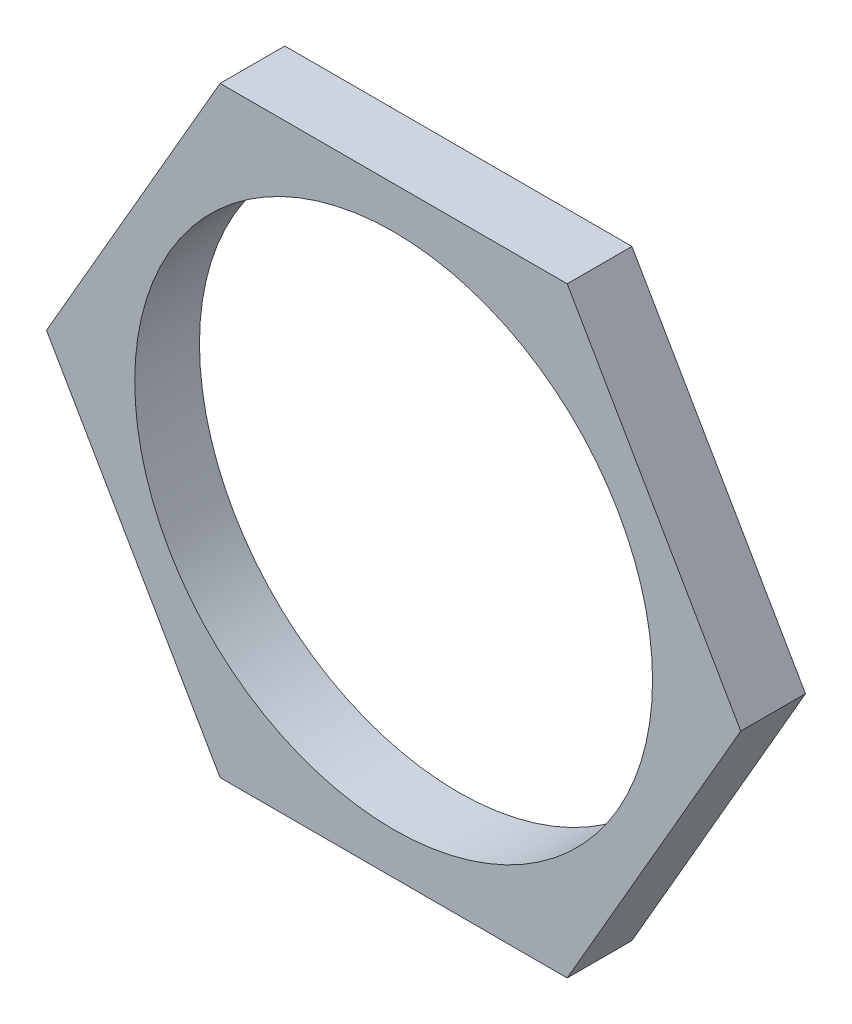
SolidWorks part; units mm, degrees
ref_plane "Ön Düzlem" through (0, 0, 0) normal (0, 0, 1) x (1, 0, 0)
ref_plane "Üst Düzlem" through (0, 0, 0) normal (0, 1, 0) x (1, 0, 0)
ref_plane "Sağ Düzlem" through (0, 0, 0) normal (1, 0, 0) x (0, 0, -1)
sketch "Sketch1" plane through (0, 0, 0) normal (0, 0, 1) x (1, 0, 0)
  line L1 (8.0441, 0) -> (4.0221, 6.9664)
  line L2 (4.0221, 6.9664) -> (-4.0221, 6.9664)
  line L3 (-4.0221, 6.9664) -> (-8.0441, 0)
  line L4 (-8.0441, 0) -> (-4.0221, -6.9664)
  line L5 (-4.0221, -6.9664) -> (4.0221, -6.9664)
  line L6 (4.0221, -6.9664) -> (8.0441, 0)
  circle A0 centre (0, 0) radius 6
  circle A1 centre (0, 0) radius 6.9664 construction
extrude "Boss-Extrude1" add sketch "Sketch1" along normal blind 1.5
